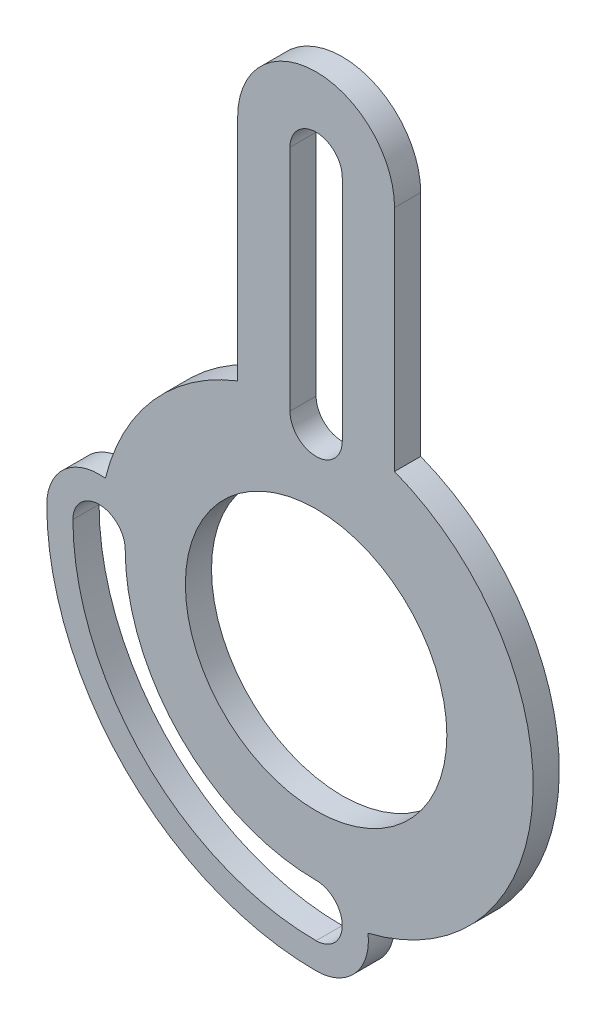
SolidWorks part; units mm, degrees
ref_plane "Front Plane" through (0, 0, 0) normal (0, 0, 1) x (1, 0, 0)
ref_plane "Top Plane" through (0, 0, 0) normal (0, 1, 0) x (1, 0, 0)
ref_plane "Right Plane" through (0, 0, 0) normal (1, 0, 0) x (0, 0, -1)
sketch "Sketch2" plane through (0, 0, 0) normal (0, 0, 1) x (1, 0, 0)
  line L0 (0, 38.69) -> (0, 82.39) construction
  line L1 (15, 82.39) -> (15, 38.6943)
  line L2 (-5, 38.69) -> (-5, 82.39)
  line L3 (5, 38.69) -> (5, 82.39)
  line L4 (-15, 82.39) -> (-15, 38.6943)
  circle A0 centre (0, 0) radius 25
  arc A1 (-5, 38.69) -> (5, 38.69) centre (0, 38.69) ccw
  arc A2 (5, 82.39) -> (-5, 82.39) centre (0, 82.39) ccw
  arc A3 (-15, 82.39) -> (15, 82.39) centre (0, 82.39) cw
  arc A4 (-41.5, 0) -> (0, -41.5) centre (0, 0) ccw construction
  arc A5 (-46.5, 0) -> (0, -46.5) centre (0, 0) ccw
  arc A6 (-36.5, 0) -> (0, -36.5) centre (0, 0) ccw
  arc A7 (-36.5, 0) -> (-46.5, 0) centre (-41.5, 0) ccw
  arc A8 (0, -46.5) -> (0, -36.5) centre (0, -41.5) ccw
  arc A9 (-51.5, 0) -> (0, -51.5) centre (0, 0) ccw
  arc A10 (0, -51.5) -> (9.9272, -40.2952) centre (0, -41.5) ccw
  arc A12 (-40.2952, 9.9272) -> (-51.5, 0) centre (-41.5, 0) ccw
  arc A13 (-15, 38.6943) -> (-40.2952, 9.9272) centre (0, 0) ccw
  arc A14 (15, 38.6943) -> (9.9272, -40.2952) centre (0, 0) cw
  arc A15 (-31.5, 0) -> (-51.5, 0) centre (-41.5, 0) ccw construction
  arc A16 (-31.5, 0) -> (0, -31.5) centre (0, 0) ccw construction
  arc A17 (0, -51.5) -> (0, -31.5) centre (0, -41.5) ccw construction
  point P7 (0, 60.54)
  point P17 (-29.3449, -29.3449)
  point P23 (0, 0)
  point P24 (0, 0)
  point P25 (0, 0)
  point P26 (0, 0)
  point P37 (0, 0)
  point P38 (0, 0)
  dimension "D1" = 50
  dimension "D2" = 5
  dimension "D5" = 15
  dimension "D6" = 5
  dimension "D7" = 41.5
  dimension "D8" = 10
  dimension "D3" = 43.7
  dimension "D4" = 38.69
extrude "Boss-Extrude1" add sketch "Sketch2" along normal blind 5
